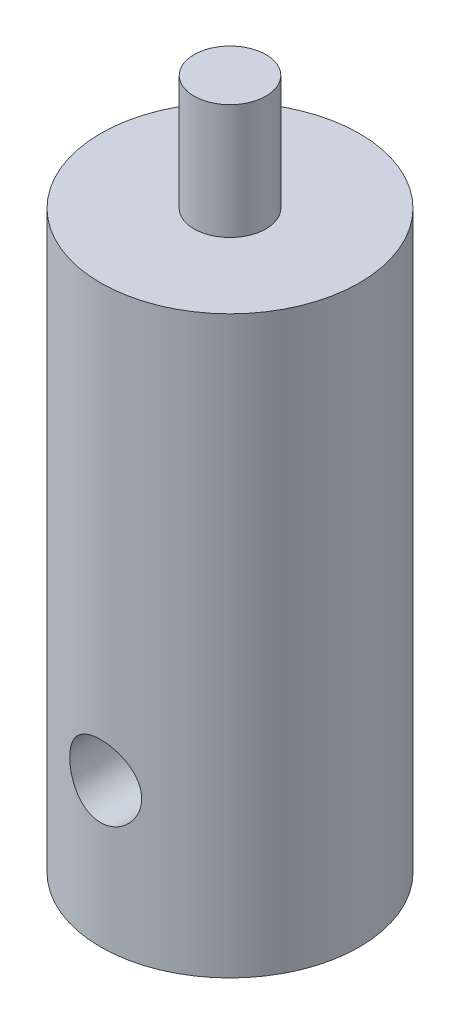
SolidWorks part; units mm, degrees
ref_plane "Front Plane" through (0, 0, 0) normal (0, 0, 1) x (1, 0, 0)
ref_plane "Top Plane" through (0, 0, 0) normal (0, 1, 0) x (1, 0, 0)
ref_plane "Right Plane" through (0, 0, 0) normal (1, 0, 0) x (0, 0, -1)
sketch "Sketch1" plane through (0, 0, 0) normal (0, 1, 0) x (1, 0, 0)
  circle A0 centre (0, 0) radius 5.715
  dimension "D1" = 11.43
extrude "Boss-Extrude1" add sketch "Sketch1" along normal blind 25.4
sketch "Sketch2" plane through (0, 25.4, 0) normal (0, 1, 0) x (1, 0, 0)
  circle A0 centre (0, 0) radius 1.5875
  dimension "D1" = 3.175
extrude "Boss-Extrude2" add sketch "Sketch2" along normal blind 5.08
ref_plane "Plane1" through (0, 0, 5.715) normal (0, 0, 1) x (1, 0, 0)
sketch "Sketch3" plane through (0, 0, 5.715) normal (0, 0, 1) x (1, 0, 0)
  circle A0 centre (0, 6.35) radius 1.5875
  dimension "D1" = 3.175
  dimension "D2" = 6.35
sketch "Sketch4" plane through (0, 0, 0) normal (0, -1, 0) x (1, 0, 0)
  circle A2 centre (0, 0) radius 1.5875
  dimension "D1" = 3.175
extrude "Cut-Extrude2" cut sketch "Sketch4" against normal blind 6.35
extrude "Cut-Extrude3" cut sketch "Sketch3" against normal through all
